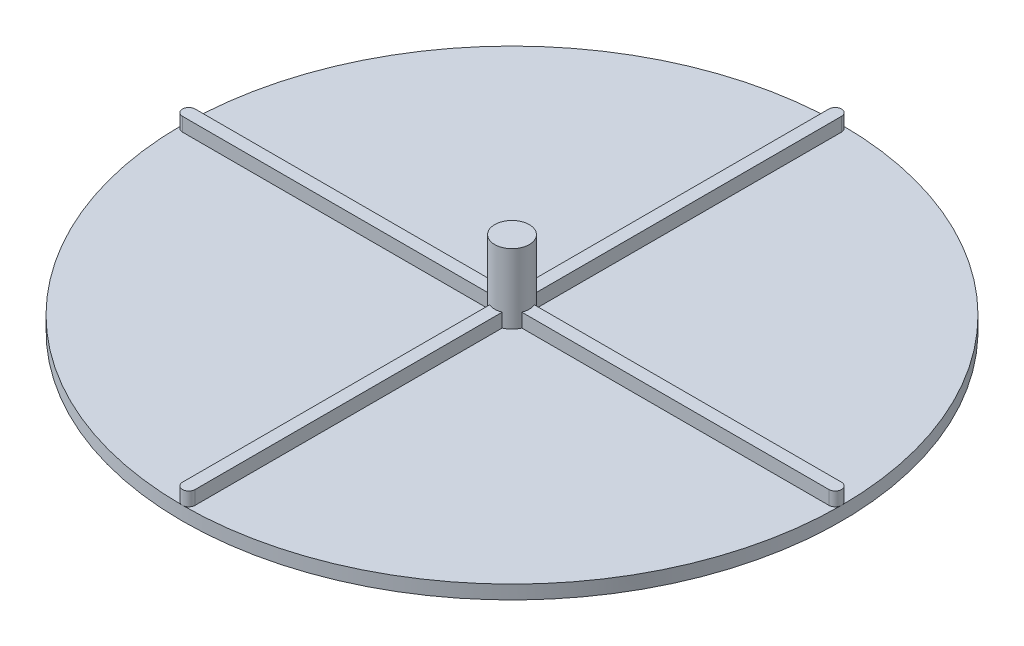
SolidWorks part; units mm, degrees
ref_plane "Front Plane" through (0, 0, 0) normal (0, 0, 1) x (1, 0, 0)
ref_plane "Top Plane" through (0, 0, 0) normal (0, 1, 0) x (1, 0, 0)
ref_plane "Right Plane" through (0, 0, 0) normal (1, 0, 0) x (0, 0, -1)
sketch "Sketch1" plane through (0, 0, 0) normal (0, 1, 0) x (1, 0, 0)
  circle A0 centre (0, 0) radius 76.2
  dimension "D1" = 152.4
extrude "Boss-Extrude1" add sketch "Sketch1" along normal blind 3.175
sketch "Sketch2" plane through (0, 3.175, 0) normal (0, 1, 0) x (1, 0, 0)
  line L0 (0, -76.2) -> (0, 76.2)
  line L1 (-76.2, 0) -> (76.2, 0)
  line L2 (-74.7395, 0) -> (74.7395, 0) construction
  line L3 (-74.7395, 1.4605) -> (74.7395, 1.4605)
  line L4 (-74.7395, -1.4605) -> (74.7395, -1.4605)
  line L5 (0, 74.7395) -> (0, -74.7395) construction
  line L6 (1.4605, 74.7395) -> (1.4605, -74.7395)
  line L7 (-1.4605, 74.7395) -> (-1.4605, -74.7395)
  circle A0 centre (0, 0) radius 76.2 construction
  arc A1 (-74.7395, 1.4605) -> (-74.7395, -1.4605) centre (-74.7395, 0) ccw
  arc A2 (74.7395, -1.4605) -> (74.7395, 1.4605) centre (74.7395, 0) ccw
  arc A3 (1.4605, 74.7395) -> (-1.4605, 74.7395) centre (0, 74.7395) ccw
  arc A4 (-1.4605, -74.7395) -> (1.4605, -74.7395) centre (0, -74.7395) ccw
  point P7 (0, 0)
  point P11 (0, 0)
  point P12 (0, 0)
  point P19 (0, 0)
  dimension "D1" = 2.921
  dimension "D2" = 2.921
extrude "Boss-Extrude2" add sketch "Sketch2" along normal blind 3.175 contours L7 A4 L6 A3 | L4 A1 L3 A2
sketch "Sketch3" plane through (0, 6.35, 0) normal (0, 1, 0) x (1, 0, 0)
  circle A0 centre (0, 0) radius 4
  dimension "D1" = 8
extrude "Boss-Extrude3" add sketch "Sketch3" along normal blind 12.954 and the other way up to surface (6.35 mm away)
